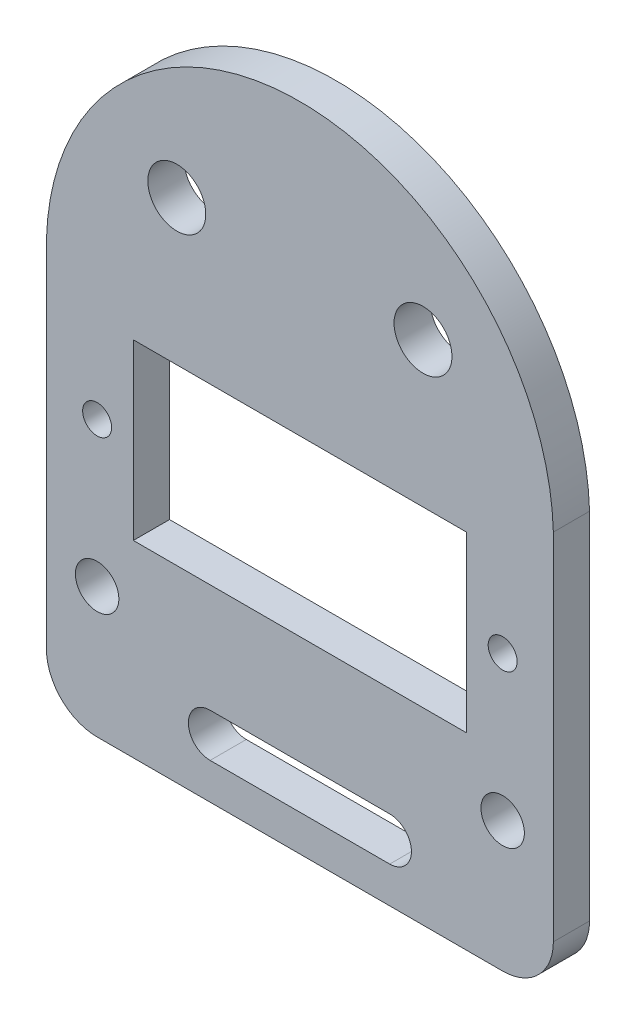
SolidWorks part; units mm, degrees
ref_plane "Front Plane" through (0, 0, 0) normal (0, 0, 1) x (1, 0, 0)
ref_plane "Top Plane" through (0, 0, 0) normal (0, 1, 0) x (1, 0, 0)
ref_plane "Right Plane" through (0, 0, 0) normal (1, 0, 0) x (0, 0, -1)
sketch "Sketch1" plane through (0, 0, 0) normal (0, 0, 1) x (1, 0, 0)
  line L0 (0, -19) -> (0, 26) construction
  line L1 (-11.5, 6) -> (11.5, 6)
  line L2 (-11.5, 6) -> (-11.5, -6)
  line L3 (-11.5, -6) -> (11.5, -6)
  line L4 (11.5, 6) -> (11.5, -6)
  line L5 (-11.5, 6) -> (11.5, -6) construction
  line L6 (-11.5, -6) -> (11.5, 6) construction
  line L7 (-6.2, -15) -> (6.2, -15) construction
  line L8 (-6.2, -13.5) -> (6.2, -13.5)
  line L9 (-6.2, -16.5) -> (6.2, -16.5)
  line L15 (-17.5, 9) -> (17.5, 9) construction
  line L16 (-17.5, 9) -> (-17.5, -19)
  line L17 (-17.5, -19) -> (17.5, -19)
  line L18 (17.5, 9) -> (17.5, -19)
  circle A0 centre (-14, 0) radius 1
  circle A1 centre (-14, -10) radius 1.5
  arc A2 (-6.2, -13.5) -> (-6.2, -16.5) centre (-6.2, -15) ccw
  arc A3 (6.2, -16.5) -> (6.2, -13.5) centre (6.2, -15) ccw
  circle A4 centre (-8.5, 16) radius 2
  circle A5 centre (14, -10) radius 1.5
  circle A6 centre (14, 0) radius 1
  circle A7 centre (8.5, 16) radius 2
  arc A8 (-17.5, 9) -> (17.5, 9) centre (0, 8.4926) cw
  point P0 (0, 0)
  point P13 (0, -15)
  point P19 (-18.5177, -5.388)
  point P27 (0, -19)
  dimension "D6" = 2
  dimension "D8" = 3
  dimension "D10" = 1.5
  dimension "D12" = 4
  dimension "D1" = 23
  dimension "D2" = 12
  dimension "D3" = 45
  dimension "D4" = 13
  dimension "D5" = 2.5
  dimension "D7" = 10
  dimension "D9" = 12.4
  dimension "D11" = 4
  dimension "D13" = 8.5
  dimension "D14" = 10
  dimension "D15" = 28
  dimension "D16" = 35
extrude "Boss-Extrude1" add sketch "Sketch1" along normal blind 2.5
fillet "Fillet1" radius 3.5 2 edges at (-17.5, -19, 1.25) (17.5, -19, 1.25)
